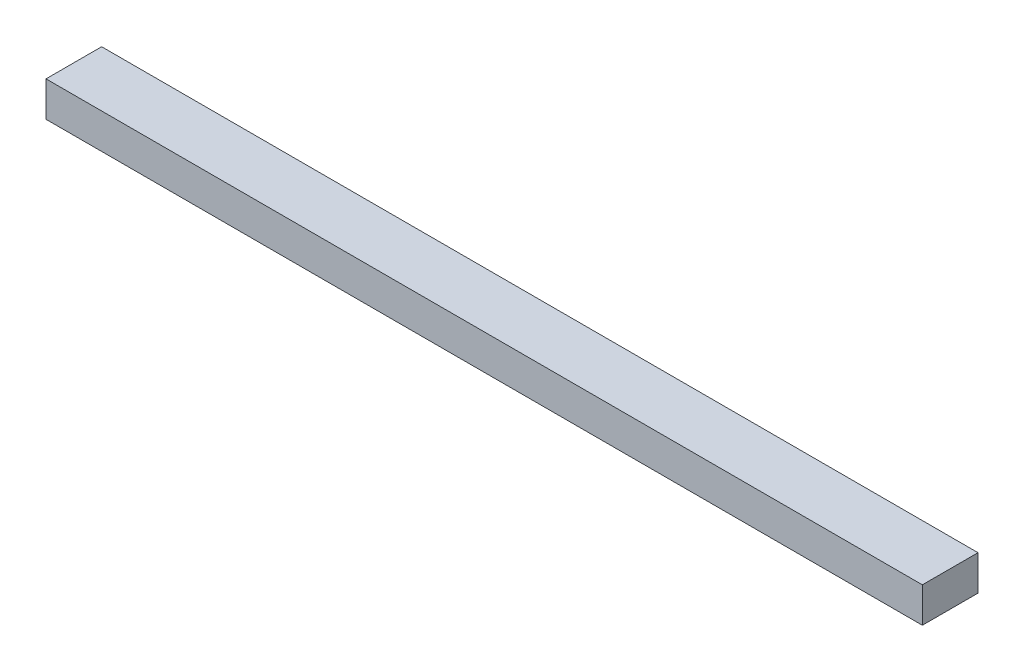
SolidWorks part; units mm, degrees
ref_plane "Front Plane" through (0, 0, 0) normal (0, 0, 1) x (1, 0, 0)
ref_plane "Top Plane" through (0, 0, 0) normal (0, 1, 0) x (1, 0, 0)
ref_plane "Right Plane" through (0, 0, 0) normal (1, 0, 0) x (0, 0, -1)
sketch "Sketch2" plane through (0, 0, 0) normal (1, 0, 0) x (0, 0, -1)
  line L1 (-6.35, 4) -> (6.35, 4)
  line L2 (-6.35, 4) -> (-6.35, -4)
  line L3 (-6.35, -4) -> (6.35, -4)
  line L4 (6.35, 4) -> (6.35, -4)
  line L5 (-6.35, 4) -> (6.35, -4) construction
  line L6 (-6.35, -4) -> (6.35, 4) construction
  point P0 (0, 0)
  dimension "D1" = 12.7
  dimension "D2" = 8
extrude "Boss-Extrude1" add sketch "Sketch2" along normal blind 200
